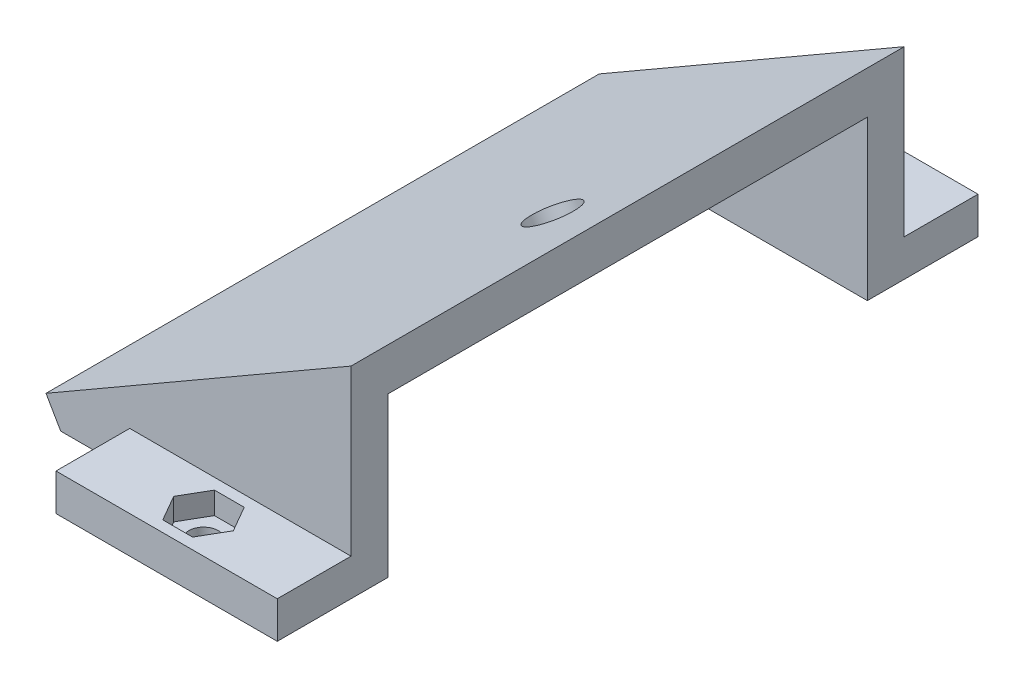
SolidWorks part; units mm, degrees
ref_plane "前视基准面" through (0, 0, 0) normal (0, 0, 1) x (1, 0, 0)
ref_plane "上视基准面" through (0, 0, 0) normal (0, 1, 0) x (1, 0, 0)
ref_plane "右视基准面" through (0, 0, 0) normal (1, 0, 0) x (0, 0, -1)
sketch "草图1" plane through (0, 0, 0) normal (0, 0, 1) x (1, 0, 0)
  line L0 (0, 0) -> (30, 0)
  line L1 (30, 0) -> (30, 27.3205)
  line L2 (30, 27.3205) -> (0, 10)
  line L3 (0, 10) -> (0, 0)
  line L4 (0, 10) -> (30, 10) construction
  dimension "D1" = 10
  dimension "D2" = 30
  dimension "D3" = 30
extrude "凸台-拉伸1" add sketch "草图1" along normal blind 75
shell "抽壳1" thickness 5
sketch "草图2" plane through (30, 0, 0) normal (1, 0, 0) x (0, 0, -1)
  line L6 (-75, 0) -> (0, 0) construction
  line L7 (-70, 5) -> (-5, 5)
  line L8 (-70, 5) -> (-70, 0)
  line L9 (-70, 0) -> (-5, 0)
  line L10 (-5, 5) -> (-5, 0)
  line L11 (-5, 5) -> (-5, 21.547) construction
extrude "切除-拉伸1" cut sketch "草图2" against normal up to surface (25 mm away) up to face at (5, 6.0566, 37.5)
sketch "草图3" plane through (-1.8301, 3.1699, 0) normal (0.5, -0.866, 0) x (0.866, 0.5, 0)
  line L0 (7.8868, 37.5) -> (27.8868, 37.5) construction
  line L1 (7.8868, 70) -> (7.8868, 5) construction
  circle A0 centre (27.8868, 37.5) radius 3.25
  dimension "D1" = 6.5
  dimension "D2" = 20
extrude "切除-拉伸2" cut sketch "草图3" against normal through all
sketch "草图4" plane through (0, 0, 75) normal (0, 0, 1) x (1, 0, 0)
  line L0 (30, 0) -> (30, 27.3205) construction
  line L1 (0, 0) -> (30, 0)
  line L2 (0, 0) -> (0, 5)
  line L3 (0, 5) -> (30, 5)
  line L4 (30, 0) -> (30, 5)
  dimension "D1" = 5
extrude "凸台-拉伸2" add sketch "草图4" along normal blind 10
ref_plane "基准面1" through (0, 0, 37.5) normal (0, 0, 1) x (1, 0, 0)
mirror "镜向1" about plane through (0, 0, 37.5) normal (0, 0, 1) of "凸台-拉伸2"
sketch "草图5" plane through (0, 0, 75) normal (0, 0, 1) x (1, 0, 0)
  line L0 (0, 10) -> (-11.3536, 3.445)
  line L1 (-11.3536, 3.445) -> (-9.3646, 0)
  line L2 (-9.3646, 0) -> (0, 0)
  line L3 (0, 0) -> (0, 10)
  line L4 (30, 27.3205) -> (0, 10) construction
  dimension "D1" = 13.11
extrude "凸台-拉伸3" add sketch "草图5" against normal up to surface (75 mm away) up to face at (15, 11.8301, 0)
sketch "草图8" plane through (0, 5, 0) normal (0, 1, 0) x (1, 0, 0)
  line L0 (30, 10) -> (0, 0) construction
  circle A0 centre (15, 5) radius 2
  dimension "D1" = 4
extrude "切除-拉伸4" cut sketch "草图8" against normal through all
sketch "草图9" plane through (0, 5, 0) normal (0, 1, 0) x (1, 0, 0)
  line L1 (17.0207, 8.5) -> (12.9793, 8.5)
  line L2 (12.9793, 8.5) -> (10.9585, 5)
  line L3 (10.9585, 5) -> (12.9793, 1.5)
  line L4 (12.9793, 1.5) -> (17.0207, 1.5)
  line L5 (17.0207, 1.5) -> (19.0415, 5)
  line L6 (19.0415, 5) -> (17.0207, 8.5)
  circle A0 centre (15, 5) radius 3.5 construction
  dimension "D1" = 7
extrude "切除-拉伸5" cut sketch "草图9" against normal blind 3
mirror "镜向2" about plane through (0, 0, 37.5) normal (0, 0, 1) of "切除-拉伸4", "切除-拉伸5"
